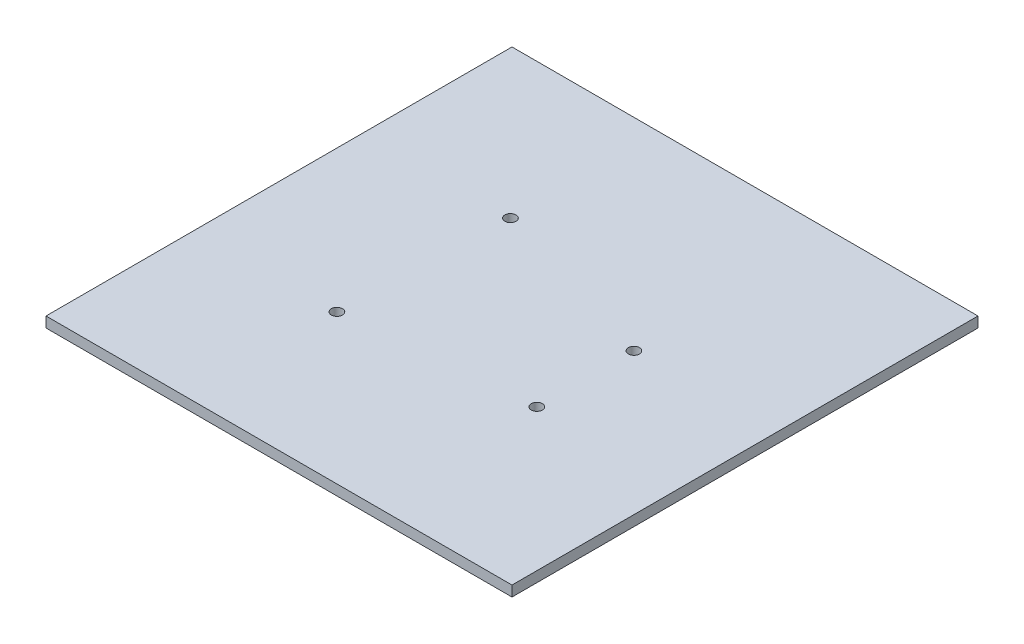
SolidWorks part; units mm, degrees
ref_plane "Front Plane" through (0, 0, 0) normal (0, 0, 1) x (1, 0, 0)
ref_plane "Top Plane" through (0, 0, 0) normal (0, 1, 0) x (1, 0, 0)
ref_plane "Right Plane" through (0, 0, 0) normal (1, 0, 0) x (0, 0, -1)
sketch "Sketch2" plane through (0, 0, 0) normal (0, 1, 0) x (1, 0, 0)
  line L0 (-67, 67) -> (67, -67)
  line L1 (-67, 67) -> (67, 67)
  line L2 (-67, 67) -> (-67, -67)
  line L3 (-67, -67) -> (67, -67)
  line L4 (67, 67) -> (67, -67)
  line L5 (67, 67) -> (-67, -67)
  line L6 (-26.2, -24.15) -> (-26.2, 24.15) construction
  line L7 (26.2, -19.05) -> (14.5033, -19.05)
  line L8 (-26.2, -24.15) -> (14.5033, -24.15)
  line L9 (14.5033, -24.15) -> (14.5033, -19.05)
  circle A0 centre (-24.6, 24.15) radius 1.6
  circle A1 centre (-26.2, -24.15) radius 1.6
  circle A2 centre (26.2, 8.85) radius 1.6
  circle A3 centre (26.2, -19.05) radius 1.6
  point P4 (0, 0)
  dimension "D2" = 3.2
  dimension "D1" = 134
  dimension "D3" = 48.3
  dimension "D4" = 40.7033
  dimension "D5" = 5.1
  dimension "D6" = 27.9
  dimension "D7" = 50.8
extrude "Boss-Extrude2" add sketch "Sketch2" along normal blind 3
